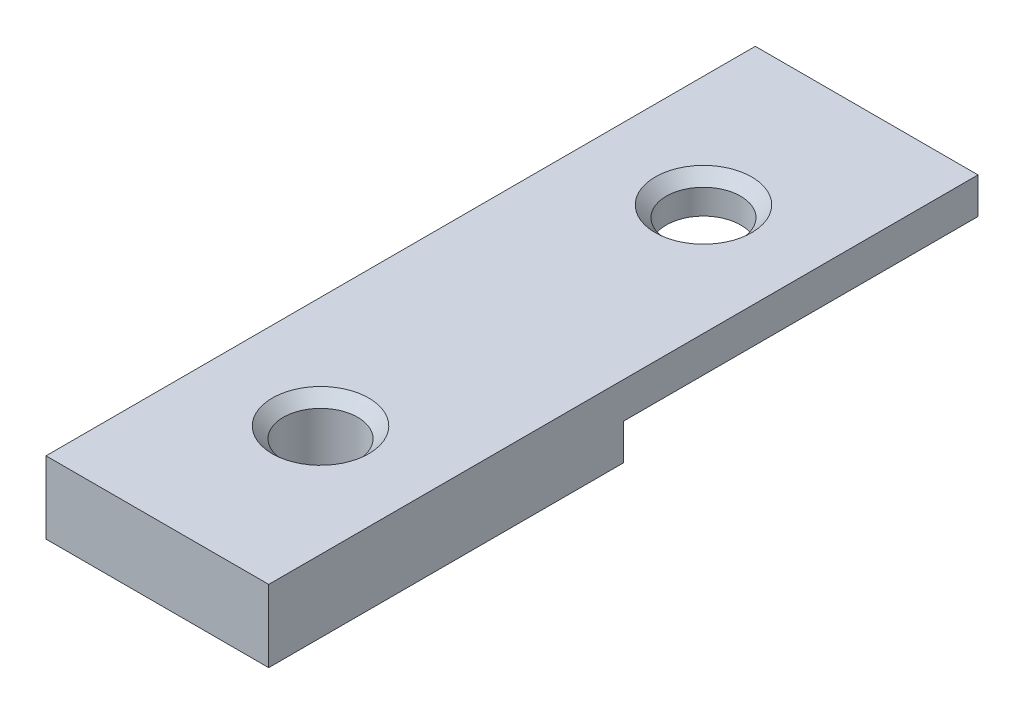
SolidWorks part; units mm, degrees
material "ABS"
ref_plane "Front Plane" through (0, 0, 0) normal (0, 0, 1) x (1, 0, 0)
ref_plane "Top Plane" through (0, 0, 0) normal (0, 1, 0) x (1, 0, 0)
ref_plane "Right Plane" through (0, 0, 0) normal (1, 0, 0) x (0, 0, -1)
sketch "Sketch1" plane through (0, 0, 0) normal (0, 1, 0) x (1, 0, 0)
  line L0 (-0.55, -0.55) -> (-20.6149, -0.55)
  line L1 (0, 0) -> (-21.1649, 0) construction
  line L2 (0, 0) -> (0, -65) construction
  line L3 (0, -65) -> (-21.1649, -65) construction
  line L4 (-21.1649, 0) -> (-21.1649, -65) construction
  line L5 (-20.6149, -0.55) -> (-20.6149, -64.45)
  line L6 (-0.55, -64.45) -> (-20.6149, -64.45)
  line L7 (-0.55, -0.55) -> (-0.55, -64.45)
  line L8 (-10.5824, 0) -> (-10.5824, -65) construction
  line L9 (-21.1649, -32.5) -> (0, -32.5) construction
  line L10 (-22.5705, 0) -> (-22.5705, -32.5)
  line L11 (-22.5705, -15.25) -> (0, -15.25) construction
  line L12 (-21.1649, 2.617) -> (-10.5824, 2.617)
  line L13 (-15.8736, 2.617) -> (-15.8736, -32.5) construction
  circle A0 centre (-10.5824, -15.25) radius 3.35
  circle A1 centre (-10.5824, -49.75) radius 3.35
  point P25 (-22.5705, -16.25)
  dimension "D6" = 6.7
  dimension "D1" = 65
  dimension "D2" = 21.1649
  dimension "D4" = 1.4056
  dimension "D5" = 2.617
  dimension "D7" = 1
  dimension "D3" = 0.55
extrude "Boss-Extrude1" add sketch "Sketch1" along normal blind 6.5 contours L7 L0 L5 L6 A0 A1
chamfer "Chamfer1" distance 1 angle 45 2 edges at (-10.5824, 6.5, 53.1) (-10.5824, 6.5, 18.6)
sketch "Sketch2" plane through (-0.55, 0, 0) normal (1, 0, 0) x (0, 0, -1)
  line L0 (-32.5, 6.5) -> (-32.5, 0) construction
  line L1 (-0.55, 6.5) -> (-64.45, 6.5) construction
  line L2 (-0.55, 0) -> (-64.45, 0) construction
  line L3 (-32.5, 3.25) -> (-0.55, 3.25)
  line L4 (-0.55, 6.5) -> (-0.55, 0) construction
  line L5 (-0.55, 3.25) -> (-0.55, 0)
  line L6 (-0.55, 0) -> (-32.5, 0)
  line L7 (-32.5, 0) -> (-32.5, 3.25)
extrude "Cut-Extrude1" cut sketch "Sketch2" against normal through all
